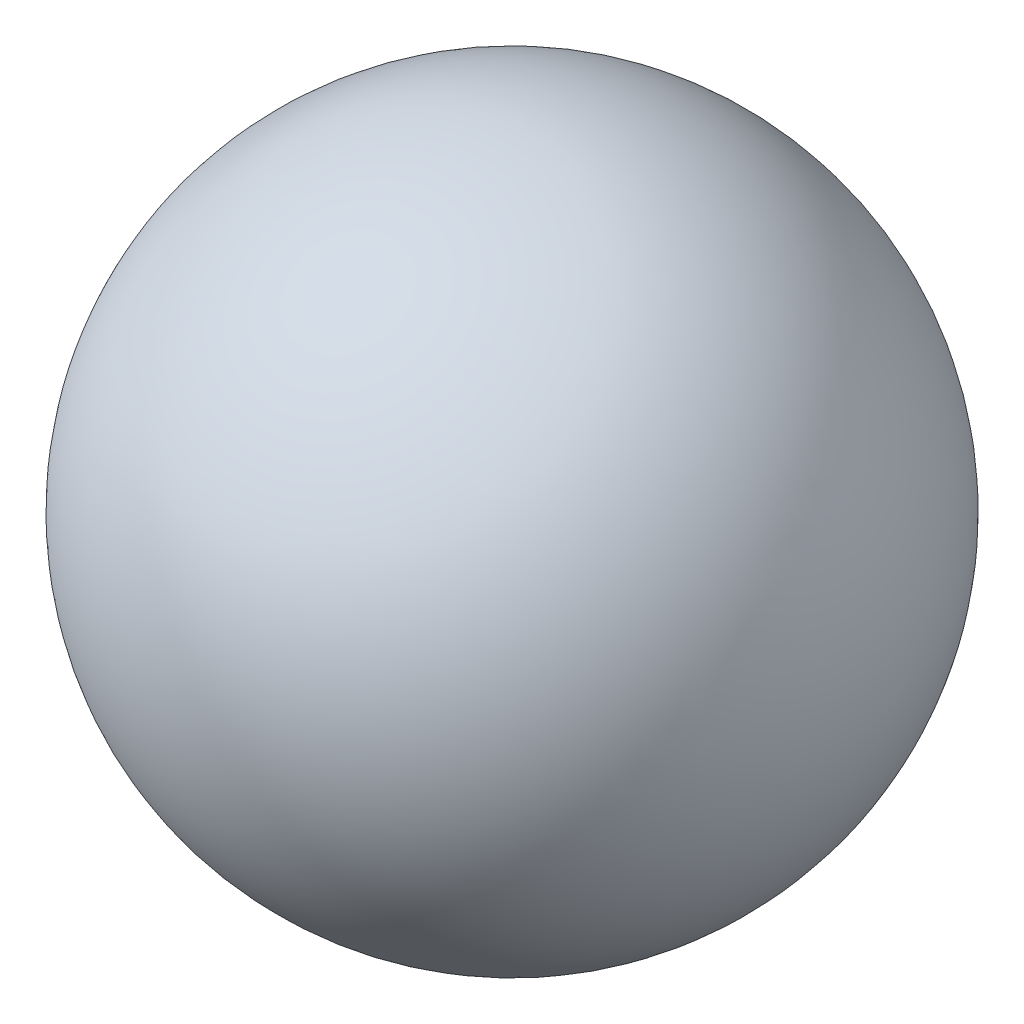
SolidWorks part; units mm, degrees
ref_plane "Front Plane" through (0, 0, 0) normal (0, 0, 1) x (1, 0, 0)
ref_plane "Top Plane" through (0, 0, 0) normal (0, 1, 0) x (1, 0, 0)
ref_plane "Right Plane" through (0, 0, 0) normal (1, 0, 0) x (0, 0, -1)
ref_plane "Plane1" through (0, 0, 0) normal (0, 0, 1) x (1, 0, 0)
sketch "Sketch1" plane through (0, 0, 0) normal (0, 0, 1) x (1, 0, 0)
  line L0 (5.882, 10) -> (1.118, 10)
  line L1 (50, 10) -> (-50, 10) construction
  arc A0 (1.118, 10) -> (5.882, 10) centre (3.5, 10) cw
revolve "Revolve1" add sketch "Sketch1" angle 360 about L1
